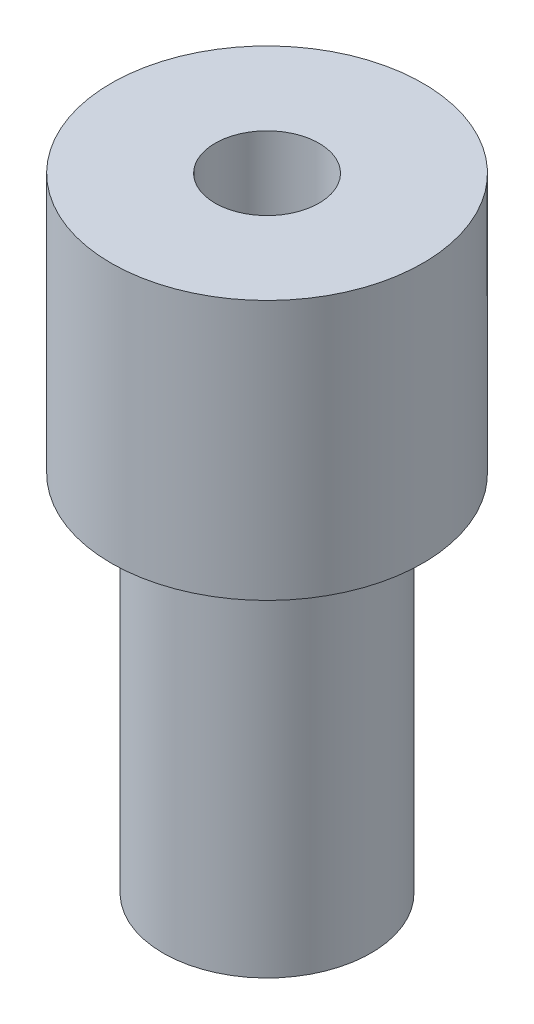
SolidWorks part; units mm, degrees
ref_plane "Front Plane" through (0, 0, 0) normal (0, 0, 1) x (1, 0, 0)
ref_plane "Top Plane" through (0, 0, 0) normal (0, 1, 0) x (1, 0, 0)
ref_plane "Right Plane" through (0, 0, 0) normal (1, 0, 0) x (0, 0, -1)
sketch "Sketch2" plane through (0, 0, 0) normal (0, 1, 0) x (1, 0, 0)
  circle A0 centre (0, 0) radius 4
  circle A1 centre (0, 0) radius 2
  dimension "D1" = 4
  dimension "D2" = 8
extrude "Boss-Extrude1" add sketch "Sketch2" along normal blind 14
sketch "Sketch3" plane through (0, 14, 0) normal (0, 1, 0) x (1, 0, 0)
  circle A0 centre (0, 0) radius 2
  circle A1 centre (0, 0) radius 6
  circle A2 centre (0, 0) radius 2 construction
  dimension "D1" = 12
extrude "Boss-Extrude2" add sketch "Sketch3" along normal blind 10
